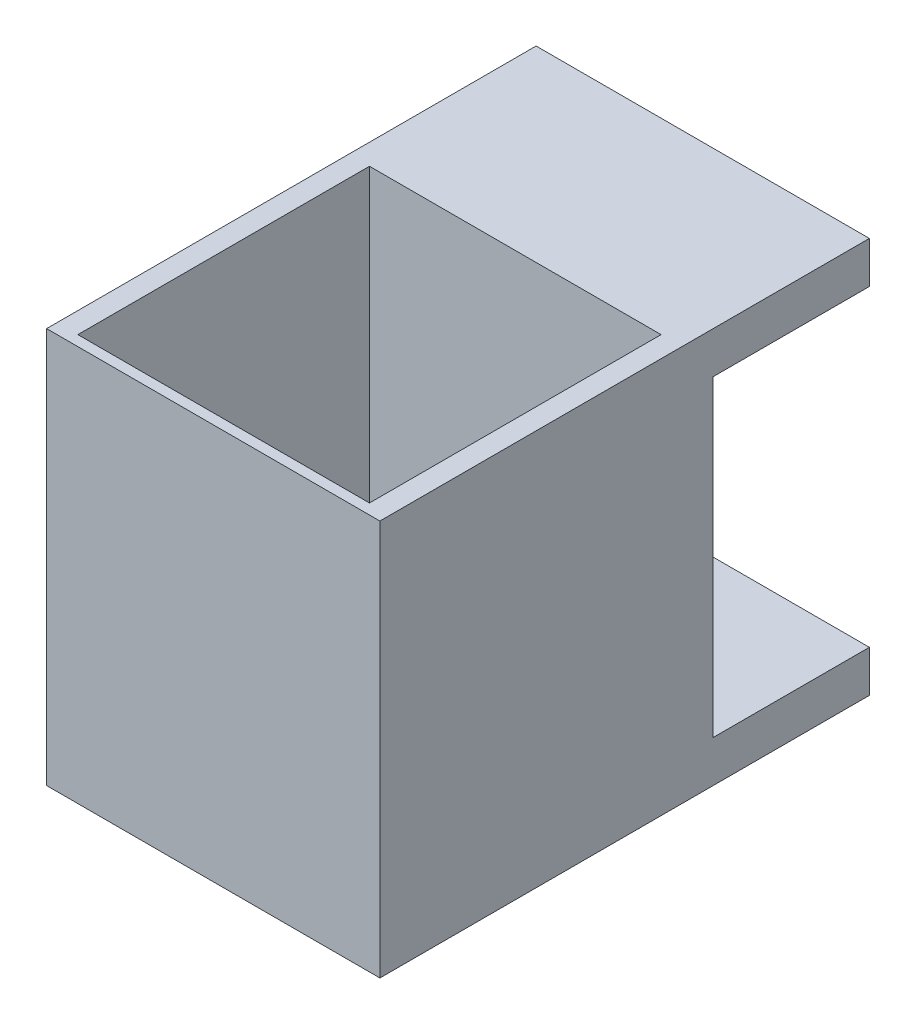
SolidWorks part; units mm, degrees
ref_plane "Front Plane" through (0, 0, 0) normal (0, 0, 1) x (1, 0, 0)
ref_plane "Top Plane" through (0, 0, 0) normal (0, 1, 0) x (1, 0, 0)
ref_plane "Right Plane" through (0, 0, 0) normal (1, 0, 0) x (0, 0, -1)
sketch "Sketch1" plane through (0, 0, 0) normal (1, 0, 0) x (0, 0, -1)
  line L0 (0, 0) -> (0, 38)
  line L1 (0, 38) -> (47, 38)
  line L2 (47, 38) -> (47, 34)
  line L3 (47, 34) -> (32, 34)
  line L4 (32, 34) -> (32, 4)
  line L5 (32, 4) -> (47, 4)
  line L6 (47, 4) -> (47, 0)
  line L7 (47, 0) -> (0, 0)
  dimension "D1" = 38
  dimension "D2" = 4
  dimension "D3" = 4
  dimension "D4" = 15
  dimension "D5" = 47
  dimension "D6" = 47
extrude "Boss-Extrude1" add sketch "Sketch1" along normal mid plane 32
sketch "Sketch2" plane through (0, 38, 0) normal (0, 1, 0) x (1, 0, 0)
  line L0 (16, 0) -> (-16, 0) construction
  line L1 (-14, 29) -> (14, 29)
  line L2 (-14, 29) -> (-14, 1)
  line L3 (-14, 1) -> (14, 1)
  line L4 (14, 29) -> (14, 1)
  line L5 (16, 47) -> (16, 0) construction
  dimension "D1" = 1
  dimension "D2" = 28
  dimension "D3" = 28
  dimension "D4" = 2
extrude "Cut-Extrude1" cut sketch "Sketch2" against normal through all
sketch "Sketch3" plane through (0, 0, -47) normal (0, 0, -1) x (-1, 0, 0)
  line L0 (-16, 34) -> (16, 34) construction
  line L1 (-16, 0) -> (16, 0) construction
  circle A0 centre (0, 36) radius 1
  circle A1 centre (0, 2) radius 1
  dimension "D1" = 2
  dimension "D2" = 2
  dimension "D3" = 2
  dimension "D4" = 2
extrude "Cut-Extrude2" cut sketch "Sketch3" against normal blind 2
